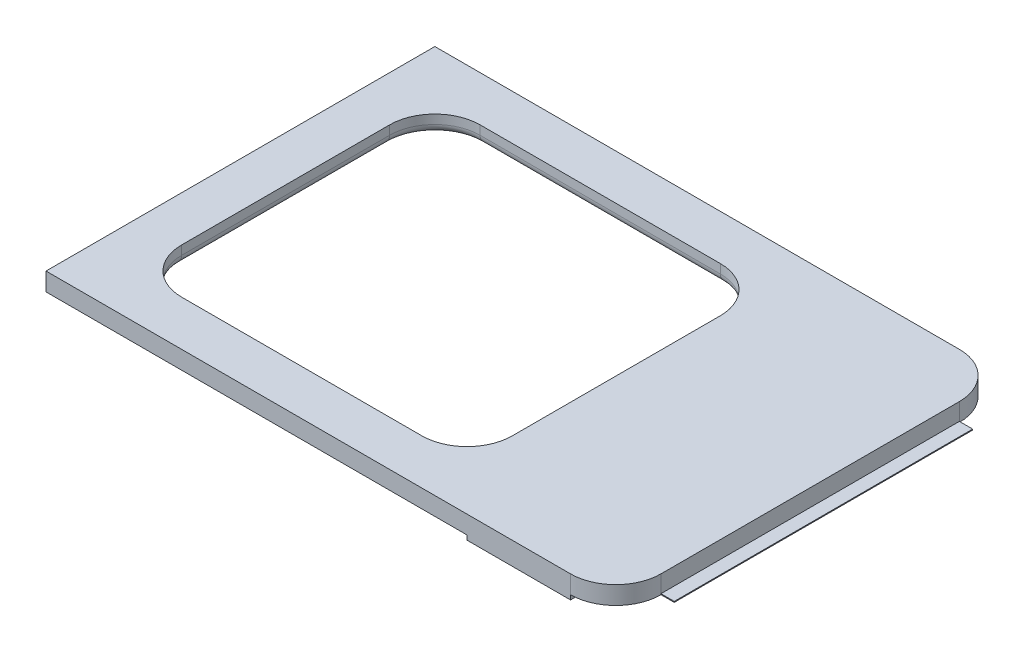
SolidWorks part; units mm, degrees
ref_plane "Front Plane" through (0, 0, 0) normal (0, 0, 1) x (1, 0, 0)
ref_plane "Top Plane" through (0, 0, 0) normal (0, 1, 0) x (1, 0, 0)
ref_plane "Right Plane" through (0, 0, 0) normal (1, 0, 0) x (0, 0, -1)
sketch "Sketch1" plane through (0, 0, 0) normal (0, 1, 0) x (1, 0, 0)
  line L0 (-26.5, 21.5) -> (-31.5, 21.5)
  line L1 (-26.5, 21.5) -> (26.5, 21.5)
  line L2 (-31.5, 16.5) -> (-31.5, -16.5)
  line L3 (-26.5, -21.5) -> (26.5, -21.5)
  line L4 (31.5, 16.5) -> (31.5, -16.5)
  line L5 (-31.5, 21.5) -> (31.5, -21.5) construction
  line L6 (-31.5, -21.5) -> (31.5, 21.5) construction
  line L7 (-31.5, 21.5) -> (-31.5, 16.5)
  line L8 (-31.5, -16.5) -> (-31.5, -21.5)
  line L9 (-31.5, -21.5) -> (-26.5, -21.5)
  arc A0 (31.5, -16.5) -> (26.5, -21.5) centre (26.5, -16.5) cw
  arc A1 (26.5, 21.5) -> (31.5, 16.5) centre (26.5, 16.5) cw
  point P0 (0, 0)
  dimension "D3" = 5
  dimension "D1" = 43
  dimension "D2" = 63
extrude "Boss-Extrude1" add sketch "Sketch1" along normal blind 2
sketch "Sketch3" plane through (0, 0, 0) normal (0, 1, 0) x (1, 0, 0)
  line L1 (31.5, -16.5) -> (32.97, -16.5)
  line L2 (31.5, -16.5) -> (31.5, 16.5)
  line L3 (31.5, 16.5) -> (32.97, 16.5)
  line L4 (32.97, -16.5) -> (32.97, 16.5)
  dimension "D1" = 1.47
extrude "Boss-Extrude3" add sketch "Sketch3" along normal blind 0.1
sketch "Sketch4" plane through (0, 0, 0) normal (0, -1, 0) x (1, 0, 0)
  line L0 (-31.5, 21.5) -> (26.5, 21.5) construction
  line L1 (26.5, 21.5) -> (15.0629, 21.5)
  line L2 (26.5, 21.5) -> (26.5, -21.5)
  line L3 (26.5, -21.5) -> (15.0629, -21.5)
  line L4 (15.0629, 21.5) -> (15.0629, -21.5)
  line L5 (26.5, -21.5) -> (-31.5, -21.5) construction
  arc A0 (31.5, 16.5) -> (26.5, 21.5) centre (26.5, 16.5) ccw construction
extrude "Boss-Extrude4" add sketch "Sketch4" along normal blind 0.5
sketch "Sketch5" plane through (0, -0.5, 0) normal (0, -1, 0) x (1, 0, 0)
  line L0 (26.5, 21.5) -> (15.0629, 21.5) construction
  line L2 (26.5, -21.5) -> (26.5, 21.5) construction
  circle A0 centre (20.7815, -10.75) radius 3.25
  circle A1 centre (20.7815, 0) radius 3.25
  circle A2 centre (20.7815, 10.75) radius 3.25
  point P8 (20.7815, 21.5)
  dimension "D4" = 6.5
  dimension "D5" = 6.5
  dimension "D6" = 6.5
  dimension "D1" = 10.75
  dimension "D2" = 10.75
  dimension "D3" = 10.75
  dimension "D7" = 5.7185
extrude "Boss-Extrude5" add sketch "Sketch5" along normal blind 1
sketch "Sketch6" plane through (0, -1.5, 0) normal (0, -1, 0) x (1, 0, 0)
  line L1 (22.7281, 9.5519) -> (20.8457, 13.0348)
  line L2 (20.8457, 13.0348) -> (18.7706, 9.6632)
  line L3 (18.7706, 9.6632) -> (22.7281, 9.5519)
  line L4 (20.7815, -2.1227) -> (22.6197, 1.0613)
  line L5 (22.6197, 1.0613) -> (18.9432, 1.0613)
  line L6 (18.9432, 1.0613) -> (20.7815, -2.1227)
  circle A0 centre (20.7815, 10.75) radius 1.1429 construction
  circle A1 centre (20.7815, 0) radius 1.0613 construction
extrude "Boss-Extrude6" add sketch "Sketch6" along normal blind 0.7
sketch "Sketch9" plane through (0, 0, 0) normal (0, -1, 0) x (-1, 0, 0)
  line L0 (-15.0629, 21.5) -> (31.5, 21.5) construction
  line L1 (-5.0629, 16.5) -> (21.5, 16.5)
  line L2 (-10.0629, 11.5) -> (-10.0629, -11.5)
  line L3 (-5.0629, -16.5) -> (21.5, -16.5)
  line L4 (26.5, 11.5) -> (26.5, -11.5)
  line L5 (31.5, 21.5) -> (31.5, -21.5) construction
  line L6 (-15.0629, -21.5) -> (-15.0629, 21.5) construction
  line L7 (31.5, -21.5) -> (-15.0629, -21.5) construction
  arc A0 (-10.0629, -11.5) -> (-5.0629, -16.5) centre (-5.0629, -11.5) ccw
  arc A1 (21.5, -16.5) -> (26.5, -11.5) centre (21.5, -11.5) ccw
  arc A2 (26.5, 11.5) -> (21.5, 16.5) centre (21.5, 11.5) ccw
  arc A3 (-10.0629, 11.5) -> (-5.0629, 16.5) centre (-5.0629, 11.5) cw
  point P6 (8.2185, 21.5)
  dimension "D5" = 5
  dimension "D1" = 5
  dimension "D2" = 5
  dimension "D3" = 5
  dimension "D4" = 5
extrude "Cut-Extrude2" cut sketch "Sketch9" against normal blind 10
fillet "Fillet4" radius 1 8 edges at (-25.0355, 0, -15.0355) (-26.5, 0, 0) (-25.0355, 0, 15.0355) (-8.2185, 0, 16.5) (8.5984, 0, 15.0355) (10.0629, 0, 0) (8.5984, 0, -15.0355) (-8.2185, 0, -16.5)
sketch "Sketch7" plane through (0, -1.5, 0) normal (0, -1, 0) x (-1, 0, 0)
  circle A0 centre (-20.7815, 10.75) radius 1.4325
extrude "Boss-Extrude7" add sketch "Sketch7" along normal blind 0.7
